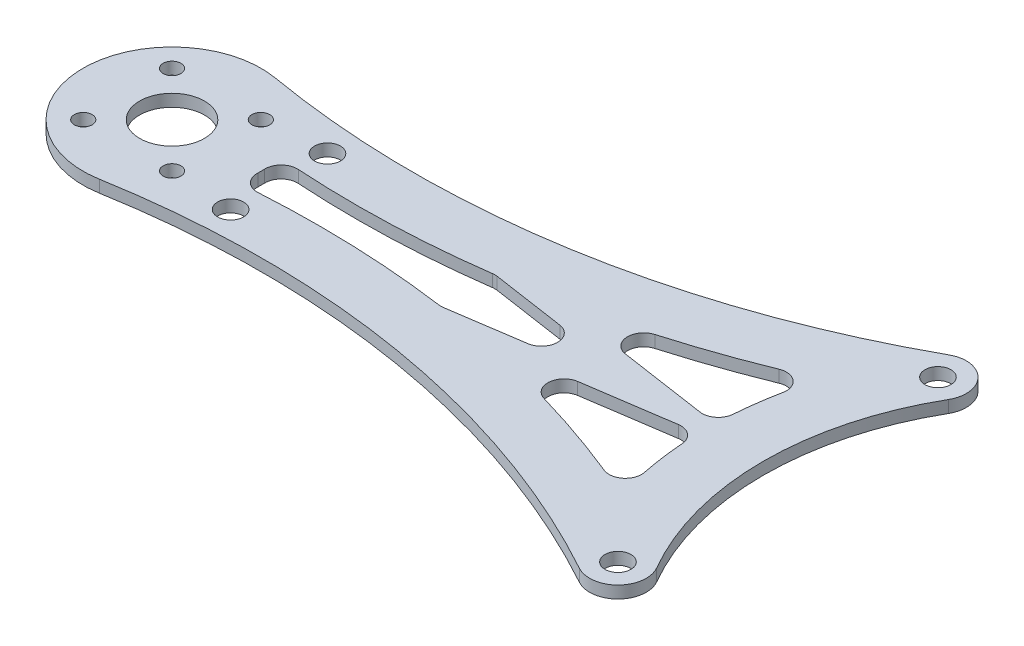
SolidWorks part; units mm, degrees
material "Thornel Mat VMA"
ref_plane "Front Plane" through (0, 0, 0) normal (0, 0, 1) x (1, 0, 0)
ref_plane "Top Plane" through (0, 0, 0) normal (0, 1, 0) x (1, 0, 0)
ref_plane "Right Plane" through (0, 0, 0) normal (1, 0, 0) x (0, 0, -1)
sketch "Sketch1" plane through (0, 0, 0) normal (0, 1, 0) x (1, 0, 0)
  line L0 (0, 0) -> (-43, 0) construction
  line L1 (0, 0) -> (-37.2391, 21.5) construction
  line L2 (0, 0) -> (-37.2391, -21.5) construction
  arc A0 (-37.2391, 21.5) -> (-37.2391, -21.5) centre (0, 0) ccw
  arc A1 (-107.1267, 10.8393) -> (-107.1267, -10.8393) centre (-109, 0) ccw
  arc A2 (-31.1769, 18) -> (-31.1769, -18) centre (0, 0) ccw
  circle A3 centre (-34.208, 19.75) radius 3.5
  circle A4 centre (-34.208, -19.75) radius 3.5
  arc A5 (-107.1267, 10.8393) -> (-35.8991, 22.8144) centre (-88.564, 118.2471) ccw
  arc A6 (-107.1267, -10.8393) -> (-35.8991, -22.8144) centre (-88.564, -118.2471) cw
  dimension "D2" = 22
  dimension "D3" = 86
  dimension "D4" = 7
  dimension "D7" = 109
  dimension "D1" = 109
  dimension "D5" = 30
  dimension "D6" = 30
  dimension "D8" = 0
extrude "Boss-Extrude1" add sketch "Sketch1" along normal mid plane 1.5 contours A1 A6 A4 A0 A3 A5 | A4 A2 A3 A0 | A4 | A3
hole_wizard "Ø2.2 (2.2) Diameter Hole1" positions "Sketch3" profile "Sketch2" hole size "Ø2.2" standard "ANSI Metric"
sketch "Sketch3" plane through (0, 0.75, 0) normal (0, 1, 0) x (1, 0, 0)
  point P39 (-114.4801, 5.4801)
  point P41 (-103.5199, 5.4801)
  point P43 (-103.5199, -5.4801)
  point P45 (-114.4801, -5.4801)
  point P48 (-101.25, 0)
sketch "Sketch2" plane through (-114.4801, 0.75, -5.4801) normal (1, 0, 0) x (0, 0, 1)
  line L0 (0, 0) -> (0, 1.5)
  line L1 (0, 1.5) -> (1.1, 1.5)
  line L2 (1.1, 1.5) -> (1.1, 0)
  line L5 (1.1, 0) -> (0, 0)
  line L11 (0, -6.35) -> (0, 107.95) construction
  dimension "Thru Hole Dia." = 2.2
  dimension "Thru Hole Depth" = 1.5
hole_wizard "Ø3.2 (3.2) Diameter Hole1" positions "Sketch5" profile "Sketch4" hole size "Ø3.2" standard "ANSI Metric"
sketch "Sketch5" plane through (0, 0.75, 0) normal (0, 1, 0) x (1, 0, 0)
  circle A0 centre (-109, 0) radius 11
  circle A1 centre (-95.7903, 5.9794) radius 3.5
  circle A2 centre (-95.7903, -5.9794) radius 3.5
  arc A3 (-35.8991, -22.8144) -> (-107.1267, -10.8393) centre (-88.564, -118.2471) ccw construction
  arc A4 (-107.1267, 10.8393) -> (-35.8991, 22.8144) centre (-88.564, 118.2471) ccw construction
  point P0 (-34.208, 19.75)
  point P3 (-34.208, -19.75)
  point P11 (-95.7903, 5.9794)
  point P13 (-95.7903, -5.9794)
  dimension "D1" = 7
sketch "Sketch4" plane through (-34.208, 0.75, -19.75) normal (1, 0, 0) x (0, 0, 1)
  line L0 (0, 0) -> (0, 10.9614)
  line L1 (0, 10.9614) -> (1.6, 10)
  line L2 (1.6, 10) -> (1.6, 0)
  line L5 (1.6, 0) -> (0, 0)
  line L10 (0, 10.9614) -> (-1.6, 10) construction
  line L11 (0, -6.35) -> (0, 107.95) construction
  dimension "Hole Dia." = 3.2
  dimension "Hole Depth" = 10
  dimension "Drill Angle" = 118
sketch "Sketch6" plane through (0, 0.75, 0) normal (0, 1, 0) x (1, 0, 0)
  line L0 (-43, 0) -> (-69.1391, -3.8851)
  line L1 (-43, 0) -> (-69.1391, 3.8851)
  line L2 (-42.853, 0.9891) -> (-68.9921, 4.8742)
  line L3 (-43.147, -0.9891) -> (-72.4693, 3.369)
  line L4 (-43.147, 0.9891) -> (-72.4693, -3.369)
  line L5 (-42.853, -0.9891) -> (-68.9921, -4.8742)
  line L6 (-43.147, -0.9891) -> (-69.2861, 2.8959) construction
  line L7 (-43.147, 0.9891) -> (-69.2861, -2.8959) construction
  arc A2 (-108.3188, 3.9416) -> (-32.5169, 16.6856) centre (-88.564, 118.2471) ccw
  arc A3 (-98.3261, 2.6586) -> (-41.184, 12.3644) centre (-88.564, 118.2471) ccw
  arc A5 (-32.5169, -16.6856) -> (-108.3188, -3.9416) centre (-88.564, -118.2471) ccw
  arc A6 (-41.184, -12.3644) -> (-98.3261, -2.6586) centre (-88.564, -118.2471) ccw
  arc A7 (-98.3261, -2.6586) -> (-98.3261, 2.6586) centre (-109, 0) ccw
  arc A8 (-37.2391, 21.5) -> (-37.2391, -21.5) centre (0, 0) ccw
  arc A9 (-41.184, 12.3644) -> (-41.184, -12.3644) centre (0, 0) ccw
  dimension "D1" = 7
  dimension "D2" = 7
  dimension "D3" = 7
  dimension "D4" = 1
  dimension "D5" = 1
  dimension "D6" = 1
  dimension "D7" = 1
extrude "Cut-Extrude1" cut sketch "Sketch6" against normal through all contours A7 A6 L4 L3 A3 | A9 A3 L2 | A9 L5 A6
fillet "Fillet1" radius 2 11 edges at (-41.184, 0, 12.3644) (-42.9882, 0, -1.0092) (-41.184, 0, -12.3644) (-42.9882, 0, 1.0092) (-66.0961, 0, -4.4438) (-66.0961, 0, 4.4438) (-49.802, 0, 0) (-72.4693, 0, 3.369) (-72.4693, 0, -3.369) (-98.3261, 0, 2.6586) (-98.3261, 0, -2.6586)
sketch "Sketch7" plane through (0, 0.75, 0) normal (0, 1, 0) x (1, 0, 0)
  circle A0 centre (-109, 0) radius 4
  dimension "D1" = 8
extrude "Cut-Extrude2" cut sketch "Sketch7" against normal through all
